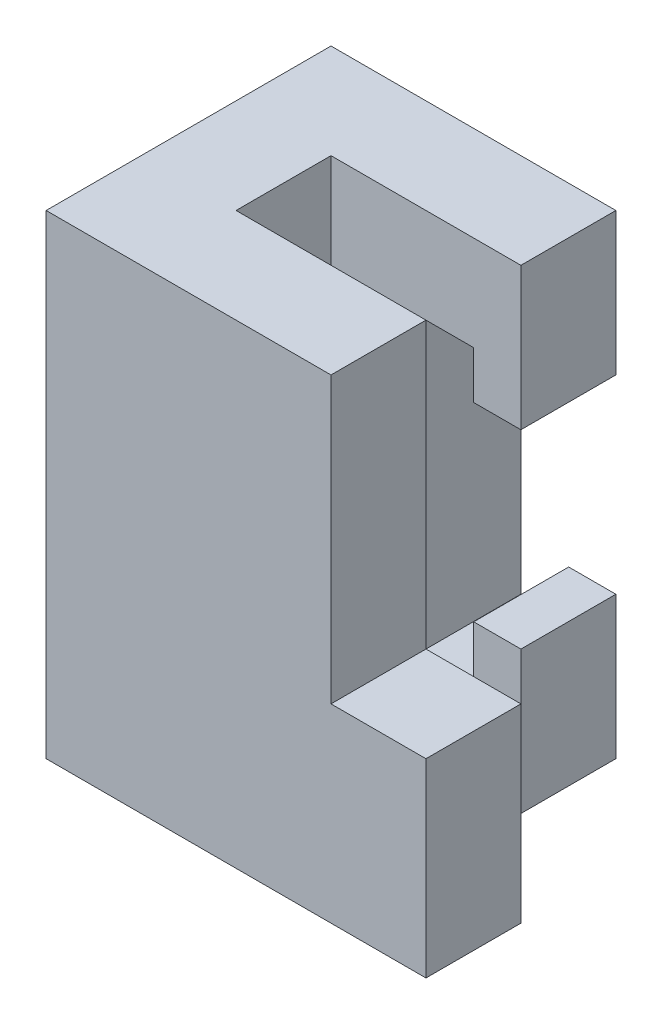
SolidWorks part; units mm, degrees
ref_plane "Front Plane" through (0, 0, 0) normal (0, 0, 1) x (1, 0, 0)
ref_plane "Top Plane" through (0, 0, 0) normal (0, 1, 0) x (1, 0, 0)
ref_plane "Right Plane" through (0, 0, 0) normal (1, 0, 0) x (0, 0, -1)
sketch "Sketch1" plane through (0, 0, 0) normal (0, 1, 0) x (1, 0, 0)
  line L0 (0, 0) -> (25.4, 0)
  line L1 (25.4, 0) -> (25.4, -12.7)
  line L2 (25.4, -12.7) -> (-12.7, -12.7)
  line L3 (-12.7, -12.7) -> (-12.7, 25.4)
  line L4 (-12.7, 25.4) -> (25.4, 25.4)
  line L5 (25.4, 25.4) -> (25.4, 12.7)
  line L6 (25.4, 12.7) -> (0, 12.7)
  line L7 (0, 12.7) -> (0, 0)
  point P9 (0, 0)
  dimension "D1" = 38.1
  dimension "D2" = 38.1
  dimension "D3" = 12.7
  dimension "D4" = 12.7
  dimension "D5" = 12.7
  dimension "D6" = 38.1
extrude "Boss-Extrude1" add sketch "Sketch1" along normal blind 63.5
sketch "Sketch2" plane through (0, 0, -25.4) normal (0, 0, -1) x (-1, 0, 0)
  line L0 (-25.4, 44.45) -> (-19.05, 44.45)
  line L1 (-25.4, 63.5) -> (-25.4, 0) construction
  line L2 (-19.05, 44.45) -> (-19.05, 50.8)
  line L3 (-19.05, 50.8) -> (-12.7, 50.8)
  line L4 (-12.7, 50.8) -> (-12.7, 12.7)
  line L5 (-12.7, 12.7) -> (-19.0887, 12.7)
  line L6 (-19.0887, 12.7) -> (-19.0887, 19.05)
  line L7 (-19.0887, 19.05) -> (-25.4, 19.05)
  line L8 (-25.4, 44.45) -> (-25.4, 19.05)
  dimension "D1" = 6.35
  dimension "D2" = 6.3113
  dimension "D3" = 12.7
  dimension "D4" = 19.05
  dimension "D5" = 12.7
  dimension "D6" = 19.05
  dimension "D7" = 12.7
extrude "Cut-Extrude3" cut sketch "Sketch2" against normal blind 12.7
sketch "Sketch3" plane through (25.4, 0, 0) normal (1, 0, 0) x (0, 0, -1)
  line L0 (0, 0) -> (0, 25.4)
  line L1 (0, 63.5) -> (0, 0) construction
  line L2 (0, 25.4) -> (-12.7, 25.4)
  line L3 (-12.7, 63.5) -> (-12.7, 0) construction
  line L4 (-12.7, 25.4) -> (-12.7, 0)
  line L5 (-12.7, 0) -> (0, 0)
  dimension "D1" = 25.4
extrude "Boss-Extrude2" add sketch "Sketch3" along normal blind 12.7
